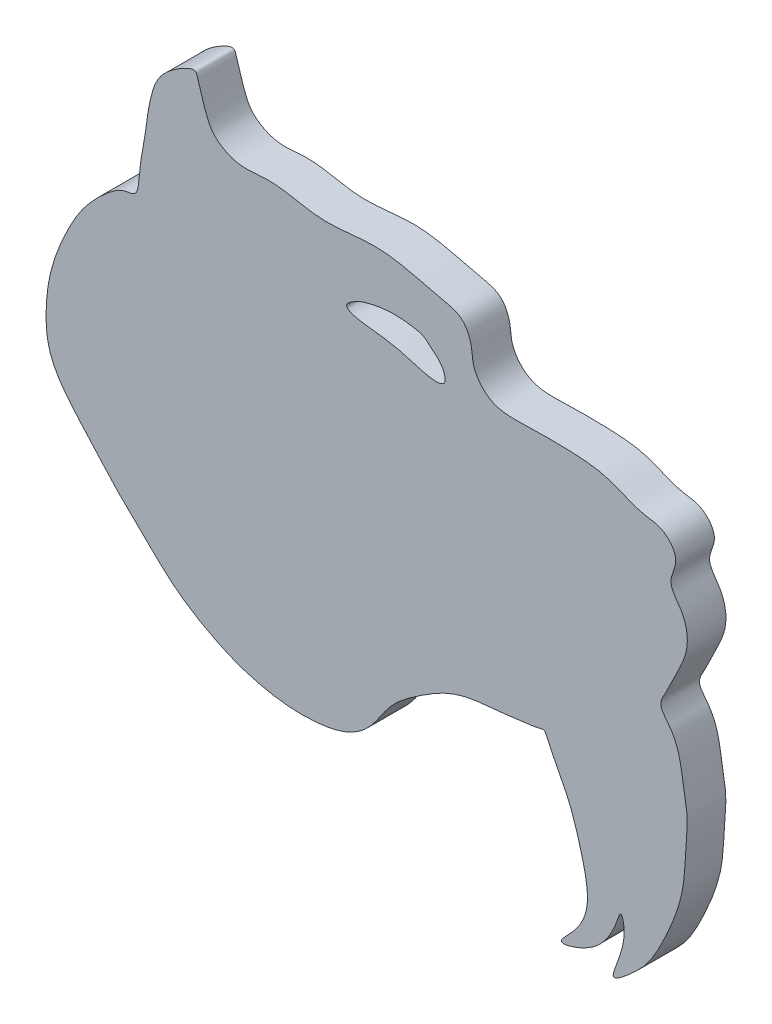
SolidWorks part; units mm, degrees
ref_plane "Спереди" through (0, 0, 0) normal (0, 0, 1) x (1, 0, 0)
ref_plane "Сверху" through (0, 0, 0) normal (0, 1, 0) x (1, 0, 0)
ref_plane "Справа" through (0, 0, 0) normal (1, 0, 0) x (0, 0, -1)
other "Configuration Table"
sketch "Sketch2" plane through (0, 0, 0) normal (0, 0, 1) x (1, 0, 0)
  spline S0 degree 3 poles (-12.5367, 21.3008) (-12.4531, 24.0427) (-11.9725, 26.1451) (-11.7382, 28.6157) (-10.881, 31.037) (-8.1651, 32.6642) (-7.9499, 32.0513) (-7.2923, 29.6681) (-6.6205, 28.5786) (-4.6206, 27.5086) (-2.0993, 28.1838) (1.7054, 26.9007) (5.1506, 27.723) (8.3733, 27.2888) (10.4248, 26.6831) (12.7553, 26.2509) (13.3675, 24.7158) (13.3998, 23.0311) (14.798, 21.255) (17.8249, 21.3651) (20.8147, 21.4015) (24.0469, 21.1454) (26.1837, 19.9197) (28.2562, 19.8367) (29.6536, 18.1855) (28.3856, 16.3853) (29.9682, 14.7849) (30.3165, 12.3089) (29.1329, 10.4277) (28.5082, 8.9032) (27.7263, 7.7745) (29.6131, 5.8875) (29.6273, 3.7304) (30.1813, 1.1319) (29.9205, -0.8096) (29.8906, -4.027) (28.7084, -7.0713) (27.3263, -9.7797) (26.0957, -11.156) (23.6243, -13.2446) (25.2661, -10.1285) (25.2171, -8.342) (24.8696, -7.6209) (24.5144, -8.9657) (23.6322, -10.4234) (22.0566, -11.7544) (19.4458, -12.4658) (21.4205, -10.8113) (22.6736, -8.5688) (21.7687, -4.7305) (21.1927, -2.9719) (20.7323, -1.8522) (18.8679, 1.7018) (19.184, 1.6185) (17.8711, 1.3516) (17.4244, 1.3462) (16.8372, 1.2299) (14.3562, 0.9488) (12.0875, 0.8404) (8.431, -1.4768) (6.4406, -3.1036) (4.8866, -6.5364) (-0.5455, -6.9224) (-4.235, -6.2008) (-6.8755, -5.0327) (-9.6564, -3.415) (-12.3862, -0.6319) (-14.199, 1.0339) (-16.4742, 3.6886) (-19.6427, 6.999) (-19.8047, 10.971) (-19.3325, 13.9157) (-17.8752, 17.208) (-16.4552, 19.4088) (-13.6425, 22.0422) (-12.5367, 21.3008) (-12.4531, 24.0427) (-11.9725, 26.1451) knots -0.057054 -0.033704 -0.011281 0 0.010468 0.0191 0.023533 0.029909 0.035689 0.044321 0.051009 0.054354 0.065246 0.079762 0.096885 0.10354 0.115516 0.121296 0.12825 0.131385 0.14025 0.149268 0.163263 0.17426 0.184589 0.189776 0.197008 0.2032 0.209601 0.218627 0.229252 0.232978 0.237623 0.242156 0.258582 0.261443 0.27076 0.280326 0.296854 0.306959 0.312535 0.320215 0.328761 0.336289 0.337574 0.341607 0.348054 0.35368 0.36781 0.375918 0.38434 0.395217 0.408547 0.416272 0.418769 0.431883 0.434978 0.446624 0.450034 0.46762 0.508042 0.528006 0.562481 0.605948 0.623742 0.638827 0.665958 0.709292 0.735428 0.764019 0.788836 0.822912 0.851947 0.887977 0.921675 0.942946 0.966296 0.988719 1 1.010468 1.0191 1.023533 only from (-12.37, 24.1349) to (-12.37, 24.1349)
extrude "Boss-Extrude1" add sketch "Sketch2" along normal blind 3 contours S0
ref_plane "Plane1" through (0, 0, 0) normal (0, 0, -1) x (-1, 0, 0)
sketch "Sketch3" plane through (0, 0, 0) normal (0, 0, -1) x (-1, 0, 0)
  spline S0 degree 3 poles (-10.445, 22.6932) (-10.1343, 22.9286) (-9.7821, 23.2946) (-9.2482, 23.5208) (-8.9186, 23.5723) (-7.2571, 23.8309) (-5.6401, 23.5643) (-4.4123, 23.1848) (-2.9156, 22.1671) (-6.1411, 21.7414) (-7.7745, 21.6196) (-11.6412, 20.1662) (-11.0893, 22.1906) (-10.445, 22.6932) (-10.1343, 22.9286) (-9.7821, 23.2946) knots -0.123046 -0.080889 -0.008089 0 0.034833 0.044236 0.094029 0.185357 0.316427 0.372439 0.425578 0.551557 0.678366 0.876954 0.919111 0.991911 1 1.034833 1.044236 1.094029 only from (-10.1999, 22.8818) to (-10.1999, 22.8818)
extrude "Cut-Extrude1" cut sketch "Sketch3" against normal blind 3
equation "\"R small\"= 2"
equation "\"R big\"= 4"
equation "\"width\"= 0.6"
equation "\"border width\"= 1"
